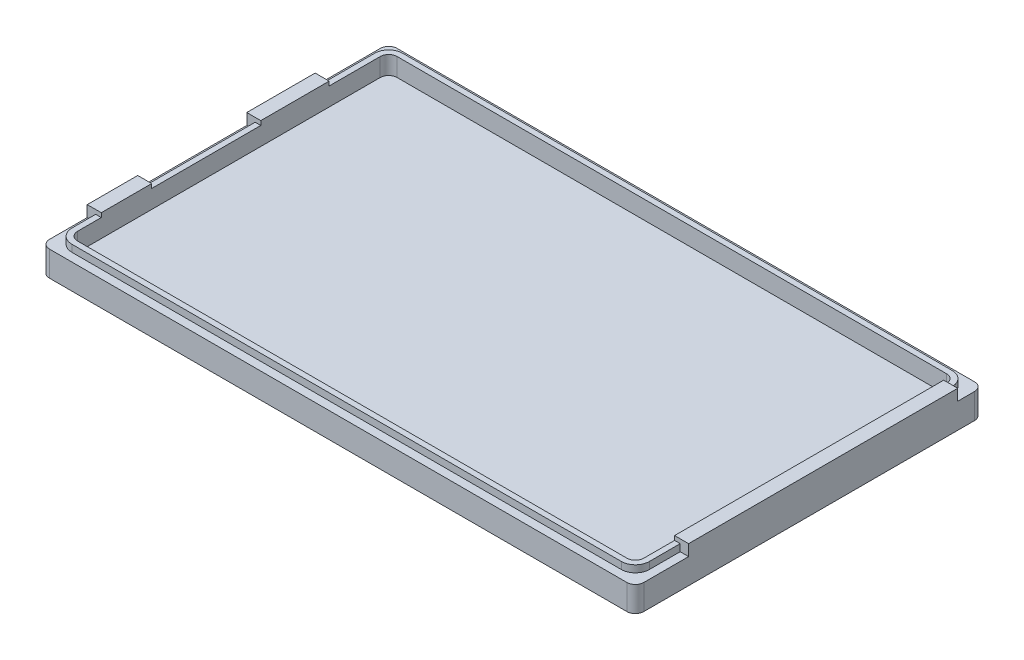
SolidWorks part; units mm, degrees
ref_plane "Front Plane" through (0, 0, 0) normal (0, 0, 1) x (1, 0, 0)
ref_plane "Top Plane" through (0, 0, 0) normal (0, 1, 0) x (1, 0, 0)
ref_plane "Right Plane" through (0, 0, 0) normal (1, 0, 0) x (0, 0, -1)
sketch "Sketch1" plane through (0, 0, 0) normal (0, 1, 0) x (1, 0, 0)
  line L1 (0, 0) -> (106, 0)
  line L2 (0, 0) -> (0, 62)
  line L3 (0, 62) -> (106, 62)
  line L4 (106, 0) -> (106, 62)
  line L5 (0, 0) -> (106, 62) construction
  line L6 (0, 62) -> (106, 0) construction
  point P4 (53, 31)
  dimension "D1" = 106
  dimension "D2" = 62
extrude "Boss-Extrude1" add sketch "Sketch1" along normal blind 2.5 contours L2 L3 L4 L1
fillet "Fillet1" radius 1.5 4 edges at (0, 1.25, -62) (106, 1.25, -62) (106, 1.25, 0) (0, 1.25, 0)
sketch "Sketch2" plane through (0, 2.5, 0) normal (0, 1, 0) x (1, 0, 0)
  line L8 (103.5, 59.5) -> (2.5, 59.5)
  line L9 (2.5, 59.5) -> (2.5, 2.5)
  line L10 (2.5, 2.5) -> (103.5, 2.5)
  line L11 (103.5, 2.5) -> (103.5, 59.5)
  line L12 (102, 59.5) -> (4, 59.5)
  line L13 (2.5, 58) -> (2.5, 4)
  line L14 (4, 2.5) -> (102, 2.5)
  line L15 (103.5, 4) -> (103.5, 58)
  line L17 (104.5, 62) -> (1.5, 62)
  line L18 (0, 60.5) -> (0, 1.5)
  line L19 (1.5, 0) -> (104.5, 0)
  line L20 (106, 1.5) -> (106, 60.5)
  line L21 (104.5, 62) -> (1.5, 62)
  line L22 (0, 60.5) -> (0, 1.5)
  line L23 (1.5, 0) -> (104.5, 0)
  line L24 (106, 1.5) -> (106, 60.5)
  arc A4 (102, 2.5) -> (103.5, 4) centre (102, 4) ccw
  arc A5 (103.5, 58) -> (102, 59.5) centre (102, 58) ccw
  arc A6 (4, 59.5) -> (2.5, 58) centre (4, 58) ccw
  arc A7 (2.5, 4) -> (4, 2.5) centre (4, 4) ccw
  arc A12 (1.5, 62) -> (0, 60.5) centre (1.5, 60.5) ccw
  arc A13 (0, 1.5) -> (1.5, 0) centre (1.5, 1.5) ccw
  arc A14 (104.5, 0) -> (106, 1.5) centre (104.5, 1.5) ccw
  arc A15 (106, 60.5) -> (104.5, 62) centre (104.5, 60.5) ccw
  arc A16 (1.5, 62) -> (0, 60.5) centre (1.5, 60.5) ccw
  arc A17 (0, 1.5) -> (1.5, 0) centre (1.5, 1.5) ccw
  arc A18 (104.5, 0) -> (106, 1.5) centre (104.5, 1.5) ccw
  arc A19 (106, 60.5) -> (104.5, 62) centre (104.5, 60.5) ccw
  dimension "D2" = 1.5
  dimension "D1" = 2.5
  dimension "D3" = 0
extrude "Boss-Extrude2" add sketch "Sketch2" along normal blind 2 contours L22 A17 L23 A18 L24 A19 L21 A16
sketch "Sketch3" plane through (0, 4.5, 0) normal (0, 1, 0) x (1, 0, 0)
  line L7 (4, 2.5) -> (102, 2.5) construction
  line L8 (103.5, 4) -> (103.5, 58) construction
  line L18 (102, 59.5) -> (4, 59.5) construction
  line L19 (2.5, 58) -> (2.5, 4) construction
  line L20 (4, 1.5) -> (102, 1.5)
  line L21 (104.5, 4) -> (104.5, 58)
  line L22 (102, 60.5) -> (4, 60.5)
  line L23 (1.5, 58) -> (1.5, 4)
  line L24 (4, 1.5) -> (102, 1.5)
  line L25 (104.5, 4) -> (104.5, 58)
  line L26 (102, 60.5) -> (4, 60.5)
  line L27 (1.5, 58) -> (1.5, 4)
  line L28 (4, 2.5) -> (102, 2.5)
  line L29 (103.5, 4) -> (103.5, 58)
  line L30 (102, 59.5) -> (4, 59.5)
  line L31 (2.5, 58) -> (2.5, 4)
  arc A17 (2.5, 4) -> (4, 2.5) centre (4, 4) ccw construction
  arc A18 (102, 2.5) -> (103.5, 4) centre (102, 4) ccw construction
  arc A19 (103.5, 58) -> (102, 59.5) centre (102, 58) ccw construction
  arc A20 (4, 59.5) -> (2.5, 58) centre (4, 58) ccw construction
  arc A21 (1.5, 4) -> (4, 1.5) centre (4, 4) ccw
  arc A22 (102, 1.5) -> (104.5, 4) centre (102, 4) ccw
  arc A23 (104.5, 58) -> (102, 60.5) centre (102, 58) ccw
  arc A24 (4, 60.5) -> (1.5, 58) centre (4, 58) ccw
  arc A25 (1.5, 4) -> (4, 1.5) centre (4, 4) ccw
  arc A26 (102, 1.5) -> (104.5, 4) centre (102, 4) ccw
  arc A27 (104.5, 58) -> (102, 60.5) centre (102, 58) ccw
  arc A28 (4, 60.5) -> (1.5, 58) centre (4, 58) ccw
  arc A29 (2.5, 4) -> (4, 2.5) centre (4, 4) ccw
  arc A30 (102, 2.5) -> (103.5, 4) centre (102, 4) ccw
  arc A31 (103.5, 58) -> (102, 59.5) centre (102, 58) ccw
  arc A32 (4, 59.5) -> (2.5, 58) centre (4, 58) ccw
  dimension "D1" = 1
extrude "Boss-Extrude3" add sketch "Sketch3" along normal blind 1.25
sketch "Sketch4" plane through (0, 4.5, 0) normal (0, 1, 0) x (1, 0, 0)
  line L0 (0, 8.24) -> (2.5, 8.24)
  line L1 (1.5, 0) -> (104.5, 0) construction
  line L2 (0, 17.24) -> (2.5, 17.24)
  line L3 (0, 48.89) -> (2.5, 48.89)
  line L4 (104.5, 62) -> (1.5, 62) construction
  line L5 (0, 36.69) -> (2.5, 36.69)
  line L6 (2.5, 58) -> (2.5, 4) construction
  line L7 (0, 60.5) -> (0, 1.5) construction
  line L8 (2.5, 48.89) -> (2.5, 36.69)
  line L9 (0, 48.89) -> (0, 36.69)
  line L10 (2.5, 17.24) -> (2.5, 8.24)
  line L11 (0, 17.24) -> (0, 8.24)
  line L12 (103.5, 4) -> (103.5, 58) construction
  line L13 (103.5, 57.5) -> (106, 57.5)
  line L14 (103.5, 57.5) -> (103.5, 9.5)
  line L15 (103.5, 9.5) -> (106, 9.5)
  line L16 (106, 57.5) -> (106, 9.5)
  line L17 (103.5, 57.5) -> (106, 9.5) construction
  line L18 (103.5, 9.5) -> (106, 57.5) construction
  line L19 (106, 1.5) -> (106, 60.5) construction
  point P20 (104.75, 33.5)
  dimension "D1" = 8.24
  dimension "D2" = 9
  dimension "D3" = 13.11
  dimension "D4" = 12.2
  dimension "D5" = 4.5
  dimension "D6" = 9.5
extrude "Boss-Extrude4" add sketch "Sketch4" along normal blind 2 contours L3 L8 L5 L9
